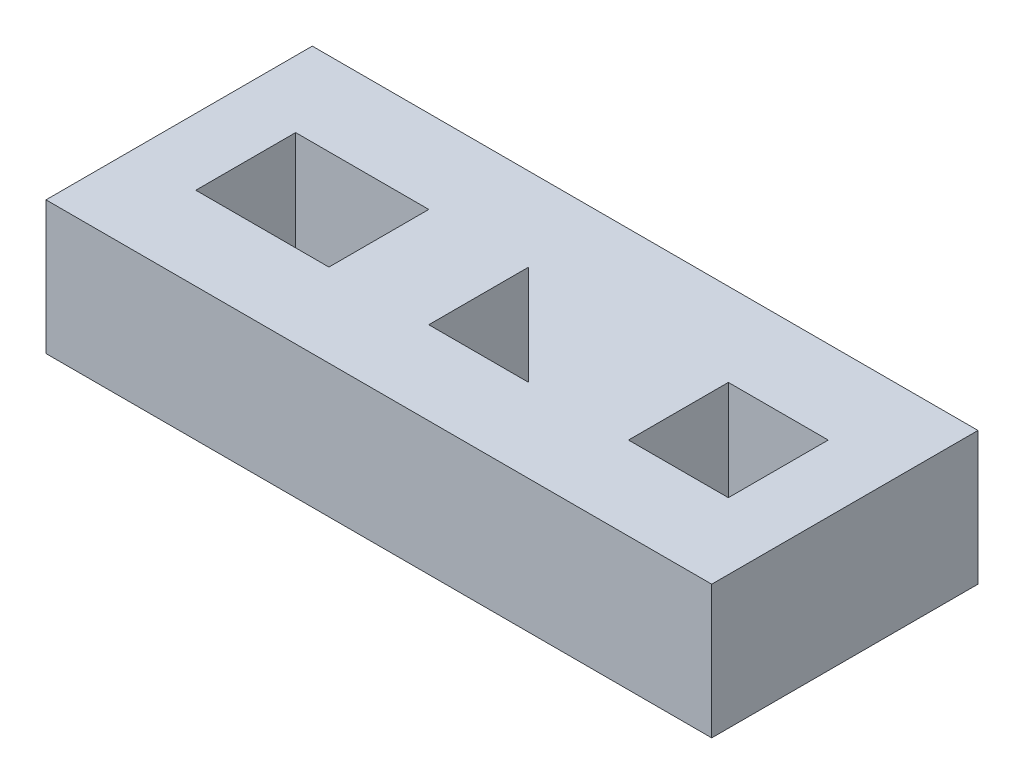
SolidWorks part; units mm, degrees
ref_plane "Front Plane" through (0, 0, 0) normal (0, 0, 1) x (1, 0, 0)
ref_plane "Top Plane" through (0, 0, 0) normal (0, 1, 0) x (1, 0, 0)
ref_plane "Right Plane" through (0, 0, 0) normal (1, 0, 0) x (0, 0, -1)
sketch "Sketch1" plane through (0, 0, 0) normal (0, 1, 0) x (1, 0, 0)
  line L1 (0, 0) -> (127, 0)
  line L2 (0, 0) -> (0, 50.8)
  line L3 (0, 50.8) -> (127, 50.8)
  line L4 (127, 0) -> (127, 50.8)
  dimension "D1" = 127
  dimension "D2" = 50.8
extrude "Boss-Extrude1" add sketch "Sketch1" along normal blind 25.4
sketch "Sketch2" plane through (0, 25.4, 0) normal (0, 1, 0) x (1, 0, 0)
  line L0 (0, 25.4) -> (127, 25.4) construction
  line L1 (0, 50.8) -> (0, 0) construction
  line L2 (127, 0) -> (127, 50.8) construction
  line L3 (57.15, 34.925) -> (57.15, 15.875)
  line L4 (12.7, 15.875) -> (38.1, 15.875)
  line L5 (12.7, 15.875) -> (12.7, 34.925)
  line L6 (12.7, 34.925) -> (38.1, 34.925)
  line L7 (38.1, 15.875) -> (38.1, 34.925)
  line L8 (95.25, 15.875) -> (114.3, 15.875)
  line L9 (95.25, 15.875) -> (95.25, 34.925)
  line L10 (95.25, 34.925) -> (114.3, 34.925)
  line L11 (114.3, 15.875) -> (114.3, 34.925)
  line L12 (57.15, 15.875) -> (76.2, 15.875)
  line L13 (76.2, 15.875) -> (57.15, 34.925)
  point P16 (12.7, 25.4)
  dimension "D1" = 25.4
  dimension "D2" = 19.05
  dimension "D3" = 12.7
  dimension "D4" = 19.05
  dimension "D5" = 12.7
extrude "Cut-Extrude1" cut sketch "Sketch2" against normal through all
